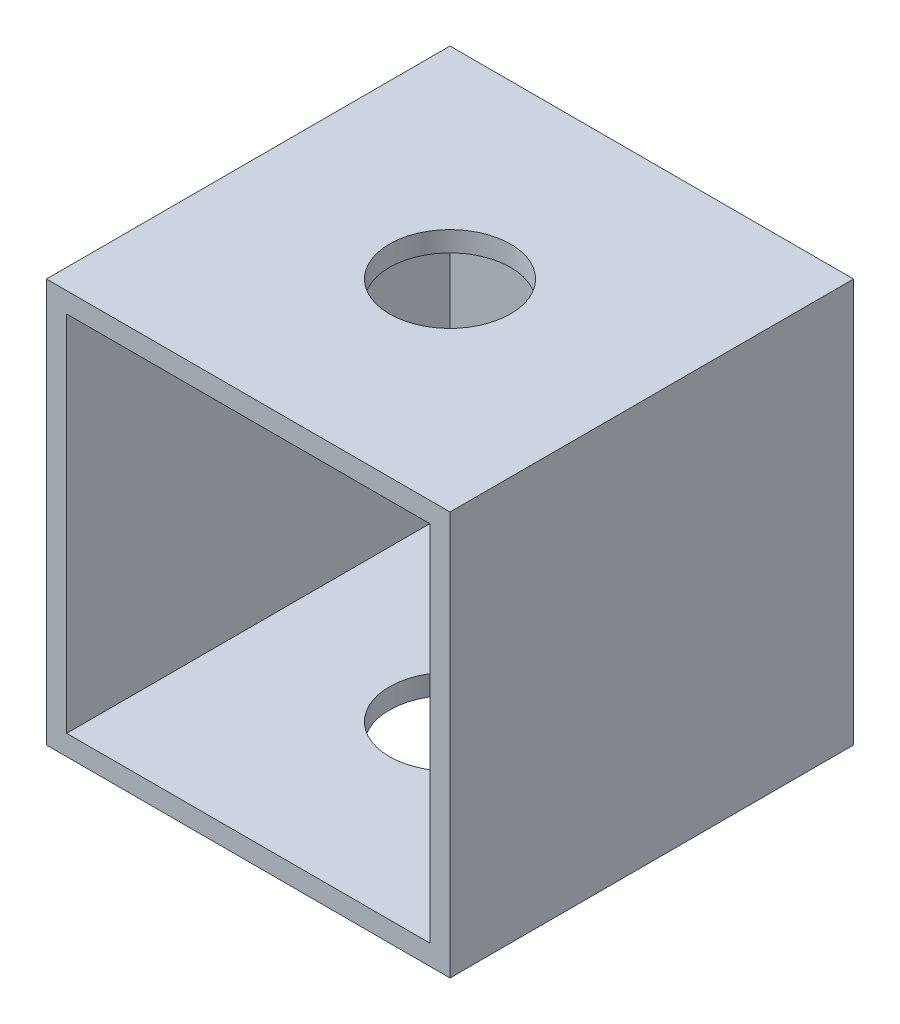
SolidWorks part; units mm, degrees
ref_plane "Front Plane" through (0, 0, 0) normal (1, 0, 0) x (0, 1, 0)
ref_plane "Top Plane" through (0, 0, 0) normal (0, 0, 1) x (0, 1, 0)
ref_plane "Right Plane" through (0, 0, 0) normal (0, 1, 0) x (-1, 0, 0)
sketch "Sketch1" plane through (0, 0, 0) normal (0, 0, 1) x (0, 1, 0)
  line L0 (-20, -20) -> (20, 20) construction
  line L1 (-20, -20) -> (20, -20)
  line L2 (-20, -20) -> (-20, 20)
  line L3 (-20, 20) -> (20, 20)
  line L4 (20, -20) -> (20, 20)
  line L5 (-20, 20) -> (20, -20) construction
  dimension "D1" = 40
  dimension "D2" = 40
extrude "Boss-Extrude1" add sketch "Sketch1" along normal blind 40
shell "Shell1" thickness 2
sketch "Sketch2" plane through (0, 20, 0) normal (0, 1, 0) x (-1, 0, 0)
  line L0 (-20, 40) -> (20, 0) construction
  line L1 (20, 40) -> (-20, 0) construction
  circle A0 centre (0, 20) radius 6
  point P10 (0, 0)
  point P11 (0, 20)
  dimension "D1" = 12
extrude "Cut-Extrude1" cut sketch "Sketch2" against normal blind 40
